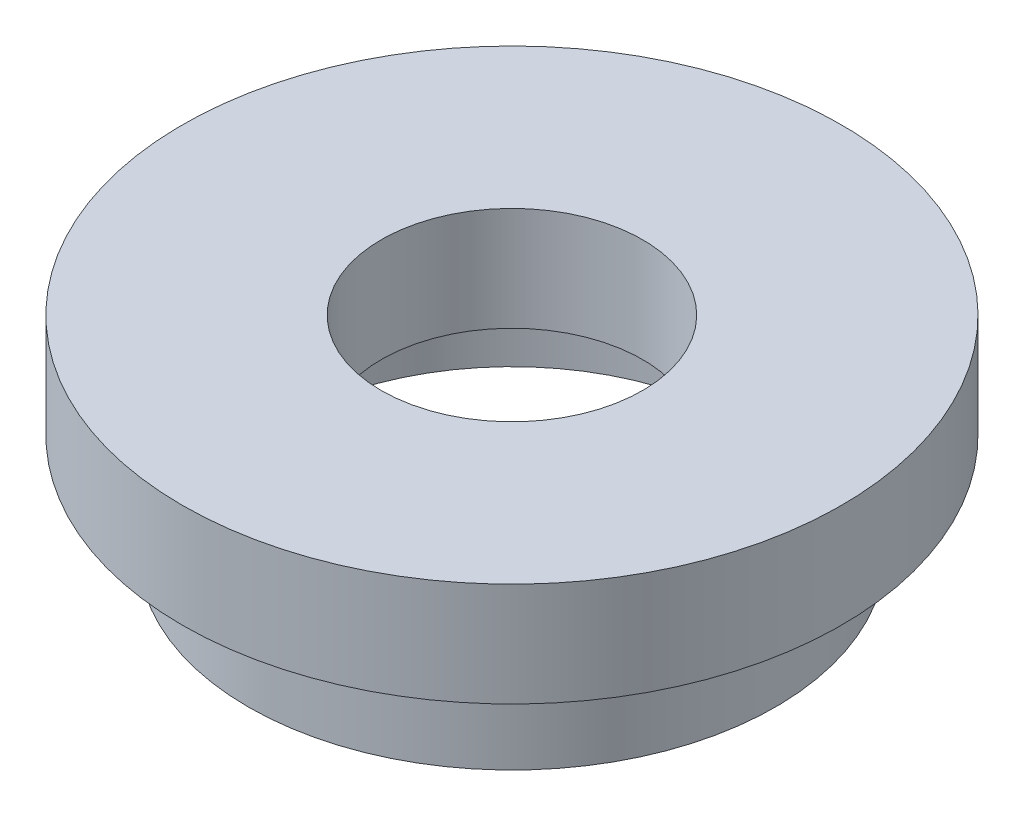
SolidWorks part; units mm, degrees
ref_plane "前视基准面" through (0, 0, 0) normal (0, 0, 1) x (1, 0, 0)
ref_plane "上视基准面" through (0, 0, 0) normal (0, 1, 0) x (1, 0, 0)
ref_plane "右视基准面" through (0, 0, 0) normal (1, 0, 0) x (0, 0, -1)
sketch "草图1" plane through (0, 0, 0) normal (0, 0, 1) x (1, 0, 0)
  line L0 (0, 13.7447) -> (0, -9.3128) construction
  line L1 (12.7, 0) -> (11.1, 0)
  line L2 (11.1, 0) -> (11.1, 4)
  line L3 (11.1, 4) -> (11.7, 4)
  line L4 (11.7, 4) -> (11.7, 5)
  line L5 (11.7, 5) -> (6.295, 5)
  line L6 (6.295, 5) -> (6.295, 10)
  line L7 (6.295, 10) -> (15.875, 10)
  line L8 (15.875, 10) -> (15.875, 5)
  line L9 (15.875, 5) -> (12.55, 5)
  line L10 (12.55, 5) -> (12.55, 4)
  line L11 (12.55, 4) -> (12.7, 4)
  line L12 (12.7, 4) -> (12.7, 0)
  dimension "D1" = 10
  dimension "D2" = 15.875
  dimension "D3" = 6.295
  dimension "D4" = 11.1
  dimension "D5" = 11.7
  dimension "D6" = 12.7
  dimension "D7" = 12.55
  dimension "D8" = 1
  dimension "D9" = 1
  dimension "D10" = 5
  dimension "D11" = 5
revolve "旋转1" add sketch "草图1" angle 360 about L0
cosmetic thread "装饰螺纹线1" parameters "D2"=13.59
cosmetic thread "装饰螺纹线2" parameters "D2"=23.2
cosmetic thread "装饰螺纹线3" parameters "D2"=24.4
